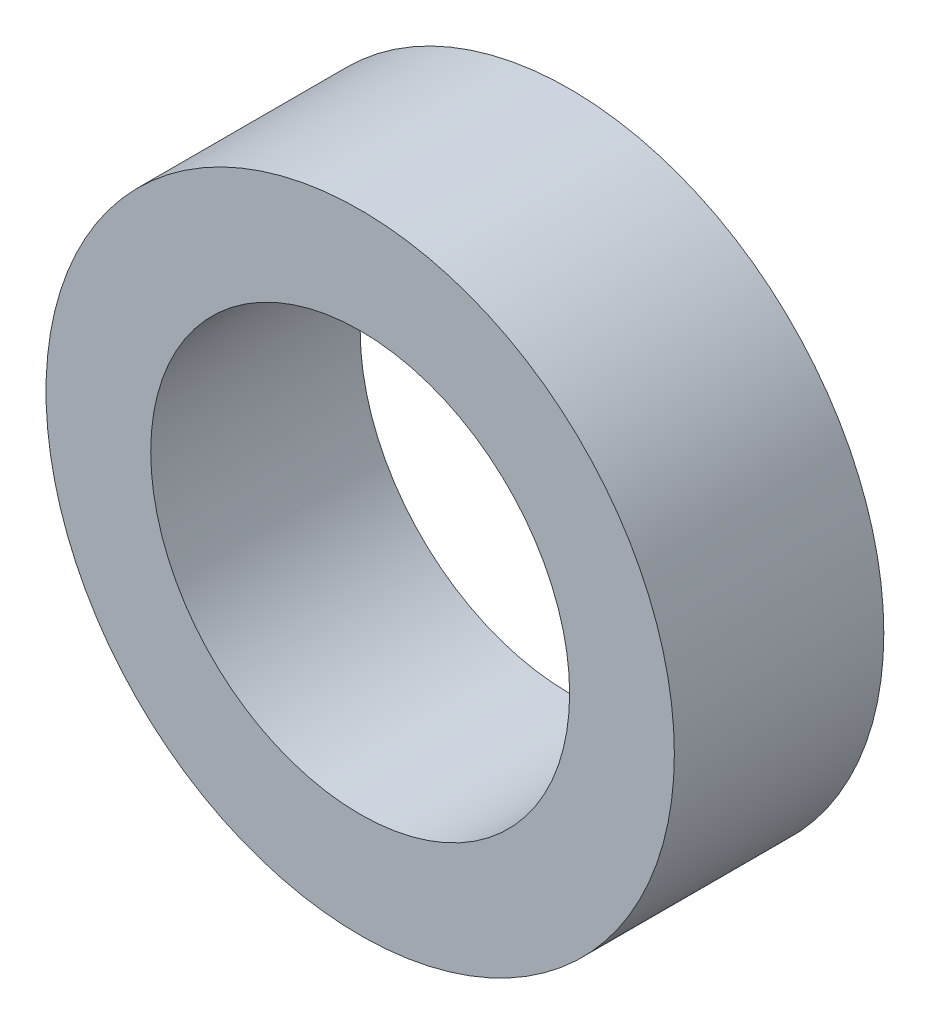
SolidWorks part; units mm, degrees
ref_plane "前视基准面" through (0, 0, 0) normal (0, 0, 1) x (1, 0, 0)
ref_plane "上视基准面" through (0, 0, 0) normal (0, 1, 0) x (1, 0, 0)
ref_plane "右视基准面" through (0, 0, 0) normal (1, 0, 0) x (0, 0, -1)
sketch "草图1" plane through (0, 0, 0) normal (0, 0, 1) x (1, 0, 0)
  circle A0 centre (0, 0) radius 5
  circle A1 centre (0, 0) radius 7.5
extrude "凸台-拉伸1" add sketch "草图1" along normal blind 5
